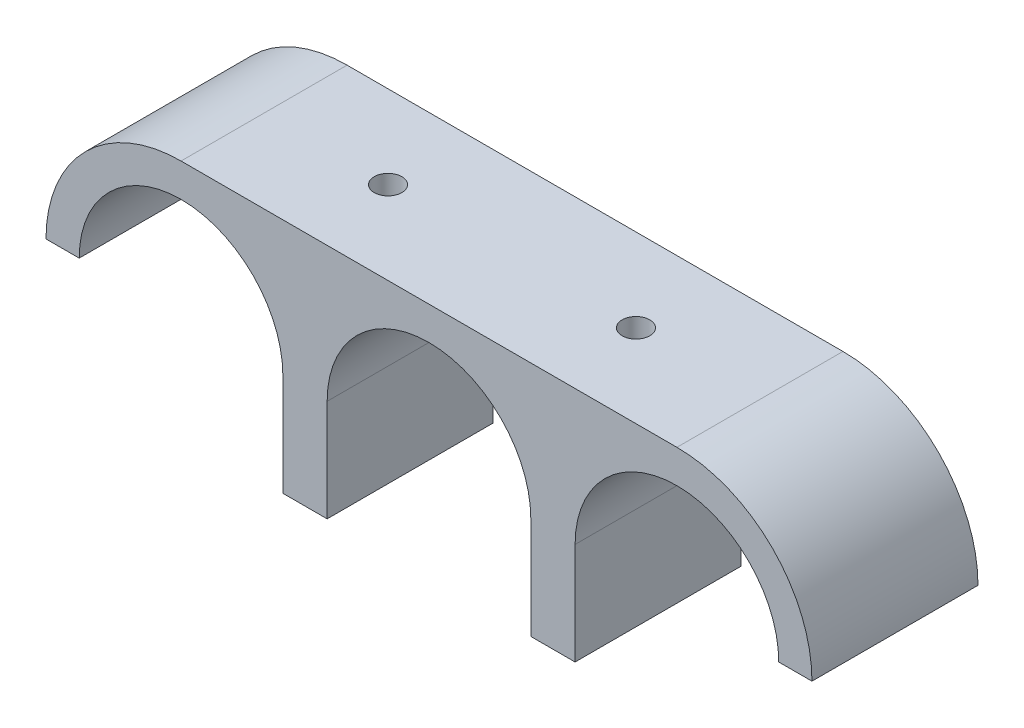
SolidWorks part; units mm, degrees
material "Aluminum"
ref_plane "Front Plane" through (0, 0, 0) normal (0, 0, 1) x (1, 0, 0)
ref_plane "Top Plane" through (0, 0, 0) normal (0, 1, 0) x (1, 0, 0)
ref_plane "Right Plane" through (0, 0, 0) normal (1, 0, 0) x (0, 0, -1)
sketch "Sketch1" plane through (0, 0, 0) normal (0, 0, 1) x (1, 0, 0)
  line L0 (4.0097, 0) -> (4.0097, 22.4253) construction
  line L1 (-30.5903, 0) -> (-27.5903, 0)
  line L2 (-18.3903, 12.2) -> (26.4097, 12.2)
  line L3 (35.6097, 0) -> (38.6097, 0)
  line L4 (-7.1903, 4.8374) -> (-7.1903, 4.8374) construction
  line L5 (-9.1903, 0) -> (-9.1903, -9.2)
  line L6 (-39.5981, 0) -> (45.7674, 0) construction
  line L7 (-9.1903, -9.2) -> (-5.1903, -9.2)
  line L8 (-9.1903, 0) -> (-5.1903, 0) construction
  line L9 (-5.1903, -9.2) -> (-5.1903, 0)
  line L10 (13.2097, 0) -> (13.2097, -9.2)
  line L11 (13.2097, -9.2) -> (17.2097, -9.2)
  line L12 (17.2097, -9.2) -> (17.2097, 0)
  arc A0 (-9.1903, 0) -> (-27.5903, 0) centre (-18.3903, 0) ccw
  arc A1 (13.2097, 0) -> (-5.1903, 0) centre (4.0097, 0) ccw
  arc A2 (35.6097, 0) -> (17.2097, 0) centre (26.4097, 0) ccw
  arc A3 (-18.3903, 12.2) -> (-30.5903, 0) centre (-18.3903, 0) ccw
  arc A4 (26.4097, 12.2) -> (38.6097, 0) centre (26.4097, 0) cw
  arc A5 (-7.1903, 4.8374) -> (-30.5903, 0) centre (-18.3903, 0) ccw construction
  arc A6 (16.2097, 0) -> (-7.1903, 4.8374) centre (4.0097, 0) ccw construction
  point P17 (26.9097, 0)
  point P19 (36.1097, 0)
  point P21 (34.7077, 2.6898)
  dimension "D1" = 18.4
  dimension "D2" = 18.4
  dimension "D6" = 18.4
  dimension "D3" = 9.2
  dimension "D5" = 9.2
  dimension "D7" = 4
  dimension "D4" = 3
extrude "Boss-Extrude1" add sketch "Sketch1" along normal blind 15
hole_wizard "Tap Drill for M3x0.5 Tap1" positions "Sketch3" profile "Sketch2" hole size "M3x0.5" standard "ANSI Metric" end condition through all
sketch "Sketch3" plane through (0, -9.2, 0) normal (0, -1, 0) x (-1, 0, 0)
  line L0 (9.1903, -15) -> (9.1903, 0) construction
  line L2 (-13.2097, -15) -> (-13.2097, 0) construction
  line L3 (9.1903, 0) -> (5.1903, 0) construction
  point P0 (7.1903, -7.5)
  point P2 (-15.2097, -7.5)
  dimension "D1" = 2
  dimension "D2" = 2
  dimension "D3" = 7.5
sketch "Sketch2" plane through (-7.1903, -9.2, 7.5) normal (1, 0, 0) x (0, 0, -1)
  line L0 (0, 0) -> (0, 21.4)
  line L1 (0, 21.4) -> (1.25, 21.4)
  line L2 (1.25, 21.4) -> (1.25, 0)
  line L5 (1.25, 0) -> (0, 0)
  line L11 (0, -6.35) -> (0, 107.95) construction
  dimension "Thru Hole Dia." = 2.5
  dimension "Thru Hole Depth" = 21.4
